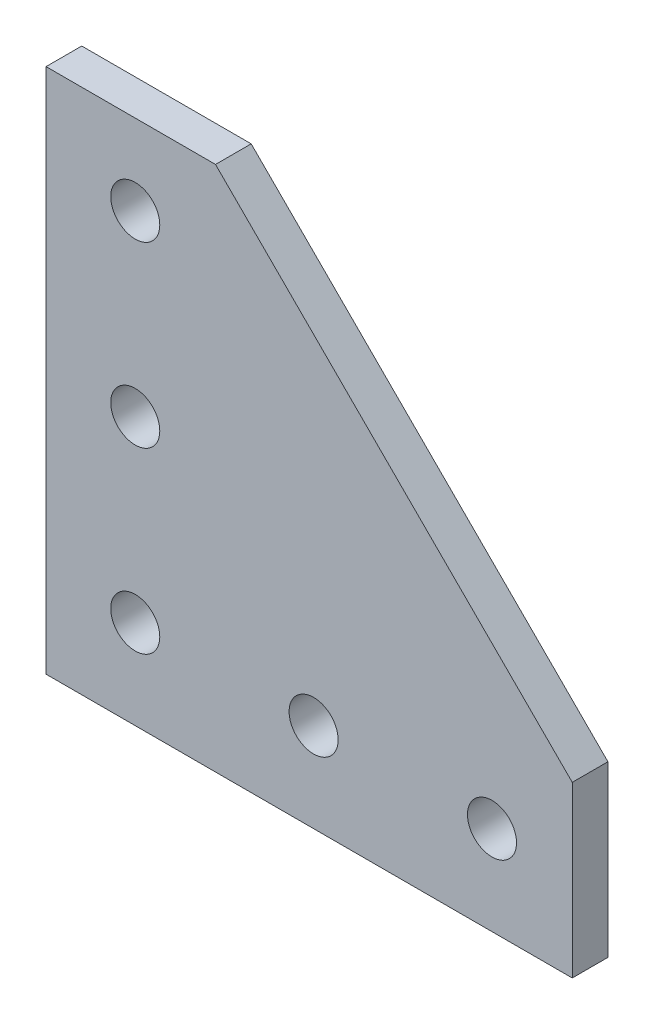
SolidWorks part; units mm, degrees
material "6063-T5"
ref_plane "Front Plane" through (0, 0, 0) normal (0, 0, 1) x (1, 0, 0)
ref_plane "Top Plane" through (0, 0, 0) normal (0, 1, 0) x (1, 0, 0)
ref_plane "Right Plane" through (0, 0, 0) normal (1, 0, 0) x (0, 0, -1)
sketch "Sketch1" plane through (0, 0, 0) normal (0, 0, 1) x (1, 0, 0)
  line L0 (0, 0) -> (0, 59)
  line L1 (0, 59) -> (19, 59)
  line L2 (19, 59) -> (59, 19)
  line L3 (59, 19) -> (59, 0)
  line L4 (59, 0) -> (0, 0)
  circle A0 centre (10, 10) radius 2.75
  circle A1 centre (10, 30) radius 2.75
  circle A2 centre (10, 50) radius 2.75
  circle A3 centre (30, 10) radius 2.75
  circle A4 centre (50, 10) radius 2.75
  dimension "D5" = 10
  dimension "D11" = 5.5
  dimension "D1" = 59
  dimension "D2" = 19
  dimension "D3" = 19
  dimension "D4" = 59
  dimension "D6" = 10
  dimension "D7" = 20
  dimension "D8" = 20
  dimension "D9" = 20
  dimension "D10" = 20
extrude "Boss-Extrude1" add sketch "Sketch1" along normal mid plane 4
